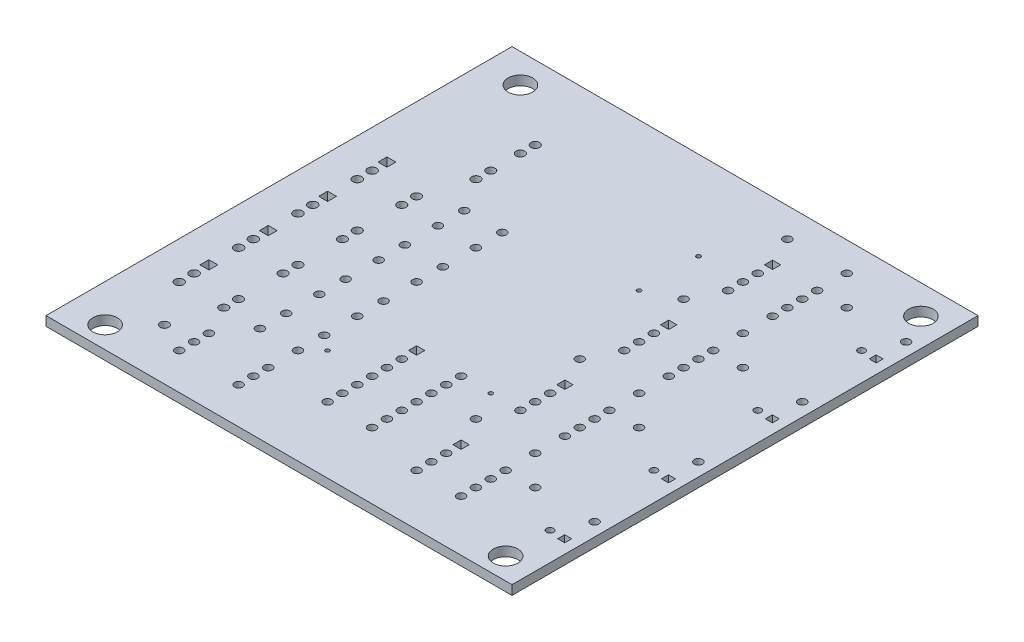
SolidWorks part; units mm, degrees
ref_plane "Front Plane" through (0, 0, 0) normal (0, 0, 1) x (1, 0, 0)
ref_plane "Top Plane" through (0, 0, 0) normal (0, 1, 0) x (1, 0, 0)
ref_plane "Right Plane" through (0, 0, 0) normal (1, 0, 0) x (0, 0, -1)
ref_plane "Plane1" through (0, 1.6, 0) normal (0, 1, 0) x (1, 0, 0)
sketch "Sketch1" plane through (0, 1.6, 0) normal (0, 1, 0) x (1, 0, 0)
  line L0 (54.1498, -45.0785) -> (55.5486, -45.0785)
  line L1 (55.5486, -45.0785) -> (55.5486, -46.4772)
  line L2 (55.5486, -46.4772) -> (54.1498, -46.4772)
  line L3 (54.1498, -46.4772) -> (54.1498, -45.0785)
  line L4 (5.7659, -37.3854) -> (7.2918, -37.3854)
  line L5 (7.2918, -37.3854) -> (7.2918, -38.9113)
  line L6 (7.2918, -38.9113) -> (5.7659, -38.9113)
  line L7 (5.7659, -38.9113) -> (5.7659, -37.3854)
  line L8 (5.7659, -57.7308) -> (7.2918, -57.7308)
  line L9 (7.2918, -57.7308) -> (7.2918, -59.2567)
  line L10 (7.2918, -59.2567) -> (5.7659, -59.2567)
  line L11 (5.7659, -59.2567) -> (5.7659, -57.7308)
  line L12 (5.7659, -27.2127) -> (7.2918, -27.2127)
  line L13 (7.2918, -27.2127) -> (7.2918, -28.7387)
  line L14 (7.2918, -28.7387) -> (5.7659, -28.7387)
  line L15 (5.7659, -28.7387) -> (5.7659, -27.2127)
  line L16 (77.097, -51.4649) -> (77.097, -50.2634)
  line L17 (77.097, -50.2634) -> (78.2985, -50.2634)
  line L18 (78.2985, -50.2634) -> (78.2985, -51.4649)
  line L19 (78.2985, -51.4649) -> (77.097, -51.4649)
  line L20 (36.3476, -52.708) -> (37.7464, -52.708)
  line L21 (37.7464, -52.708) -> (37.7464, -54.1068)
  line L22 (37.7464, -54.1068) -> (36.3476, -54.1068)
  line L23 (36.3476, -54.1068) -> (36.3476, -52.708)
  line L24 (5.7659, -47.5581) -> (7.2918, -47.5581)
  line L25 (7.2918, -47.5581) -> (7.2918, -49.084)
  line L26 (7.2918, -49.084) -> (5.7659, -49.084)
  line L27 (5.7659, -49.084) -> (5.7659, -47.5581)
  line L28 (54.1498, -62.8807) -> (55.5486, -62.8807)
  line L29 (55.5486, -62.8807) -> (55.5486, -64.2795)
  line L30 (55.5486, -64.2795) -> (54.1498, -64.2795)
  line L31 (54.1498, -64.2795) -> (54.1498, -62.8807)
  line L32 (54.1498, -27.2763) -> (55.5486, -27.2763)
  line L33 (55.5486, -27.2763) -> (55.5486, -28.6751)
  line L34 (55.5486, -28.6751) -> (54.1498, -28.6751)
  line L35 (54.1498, -28.6751) -> (54.1498, -27.2763)
  line L36 (54.1498, -9.4741) -> (55.5486, -9.4741)
  line L37 (55.5486, -9.4741) -> (55.5486, -10.8729)
  line L38 (55.5486, -10.8729) -> (54.1498, -10.8729)
  line L39 (54.1498, -10.8729) -> (54.1498, -9.4741)
  line L40 (77.097, -15.8606) -> (77.097, -14.6591)
  line L41 (77.097, -14.6591) -> (78.2985, -14.6591)
  line L42 (78.2985, -14.6591) -> (78.2985, -15.8606)
  line L43 (78.2985, -15.8606) -> (77.097, -15.8606)
  line L44 (77.097, -69.2671) -> (77.097, -68.0656)
  line L45 (77.097, -68.0656) -> (78.2985, -68.0656)
  line L46 (78.2985, -68.0656) -> (78.2985, -69.2671)
  line L47 (78.2985, -69.2671) -> (77.097, -69.2671)
  line L48 (77.097, -33.6627) -> (77.097, -32.4612)
  line L49 (77.097, -32.4612) -> (78.2985, -32.4612)
  line L50 (78.2985, -32.4612) -> (78.2985, -33.6627)
  line L51 (78.2985, -33.6627) -> (77.097, -33.6627)
  line L52 (79.9984, -0.1017) -> (0.1017, -0.1017)
  line L53 (0.1017, -0.1017) -> (0.1017, -79.9984)
  line L54 (0.1017, -79.9984) -> (79.9984, -79.9984)
  line L55 (79.9984, -79.9984) -> (79.9984, -0.1017)
  circle A0 centre (26.8743, -48.9018) radius 0.6994
  circle A1 centre (54.8492, -53.4074) radius 0.6994
  circle A2 centre (26.8743, -53.4075) radius 0.6994
  circle A3 centre (75.1944, -50.8641) radius 0.6008
  circle A4 centre (77.7378, -45.7779) radius 0.6994
  circle A5 centre (62.4787, -40.6915) radius 0.6994
  circle A6 centre (52.306, -40.6915) radius 0.6994
  circle A7 centre (62.4787, -53.4074) radius 0.6994
  circle A8 centre (6.5288, -61.0369) radius 0.763
  circle A9 centre (54.8492, -50.8642) radius 0.6994
  circle A10 centre (6.5288, -50.8642) radius 0.763
  circle A11 centre (62.4787, -48.321) radius 0.6994
  circle A12 centre (54.8492, -48.321) radius 0.6994
  circle A13 centre (62.4787, -45.7779) radius 0.6994
  circle A14 centre (6.5288, -53.4074) radius 0.763
  circle A15 centre (16.7015, -20.3462) radius 0.7375
  circle A16 centre (16.7015, -22.8894) radius 0.7375
  circle A17 centre (29.415, -61.0603) radius 0.3504
  circle A18 centre (47.2265, -15.251) radius 0.3504
  circle A19 centre (47.2265, -25.4395) radius 0.3504
  circle A20 centre (67.5651, -45.7779) radius 0.6994
  circle A21 centre (6.5288, -63.5801) radius 0.763
  circle A22 centre (75.1945, -5.0871) radius 2.1026
  circle A23 centre (75.1945, -76.2959) radius 2.1026
  circle A24 centre (20.366, -53.4075) radius 0.6994
  circle A25 centre (6.5288, -76.2959) radius 2.1026
  circle A26 centre (6.5288, -5.0871) radius 2.1026
  circle A27 centre (14.1583, -63.5801) radius 0.7375
  circle A28 centre (6.5288, -30.5189) radius 0.763
  circle A29 centre (14.1583, -50.8642) radius 0.7375
  circle A30 centre (14.1583, -53.4074) radius 0.7375
  circle A31 centre (14.1583, -40.6915) radius 0.7375
  circle A32 centre (14.1583, -43.2347) radius 0.7375
  circle A33 centre (62.4787, -50.8642) radius 0.6994
  circle A34 centre (14.1583, -61.0369) radius 0.7375
  circle A35 centre (14.1583, -30.5189) radius 0.7375
  circle A36 centre (11.6152, -71.2096) radius 0.7375
  circle A37 centre (14.1583, -33.0621) radius 0.7375
  circle A38 centre (16.7015, -12.7167) radius 0.7375
  circle A39 centre (16.7015, -15.2598) radius 0.7375
  circle A40 centre (26.8742, -71.2096) radius 0.6994
  circle A41 centre (16.7015, -71.2096) radius 0.6994
  circle A42 centre (20.366, -48.9018) radius 0.6994
  circle A43 centre (37.047, -55.9506) radius 0.6994
  circle A44 centre (44.6765, -55.9506) radius 0.6994
  circle A45 centre (37.047, -58.4937) radius 0.6994
  circle A46 centre (44.6765, -58.4937) radius 0.6994
  circle A47 centre (37.047, -61.0369) radius 0.6994
  circle A48 centre (44.6765, -61.0369) radius 0.6994
  circle A49 centre (37.047, -63.5801) radius 0.6994
  circle A50 centre (44.6765, -63.5801) radius 0.6994
  circle A51 centre (37.047, -66.1233) radius 0.6994
  circle A52 centre (44.6765, -66.1233) radius 0.6994
  circle A53 centre (37.047, -68.6664) radius 0.6994
  circle A54 centre (44.6765, -68.6664) radius 0.6994
  circle A55 centre (62.4787, -63.5801) radius 0.6994
  circle A56 centre (54.8492, -66.1233) radius 0.6994
  circle A57 centre (62.4787, -66.1233) radius 0.6994
  circle A58 centre (54.8492, -68.6664) radius 0.6994
  circle A59 centre (62.4787, -68.6664) radius 0.6994
  circle A60 centre (54.8492, -71.2096) radius 0.6994
  circle A61 centre (62.4787, -71.2096) radius 0.6994
  circle A62 centre (52.306, -58.4937) radius 0.6994
  circle A63 centre (62.4787, -58.4937) radius 0.6994
  circle A64 centre (16.7015, -73.7528) radius 0.6994
  circle A65 centre (26.8742, -73.7528) radius 0.6994
  circle A66 centre (62.4787, -27.9757) radius 0.6994
  circle A67 centre (54.8492, -30.5189) radius 0.6994
  circle A68 centre (62.4787, -30.5189) radius 0.6994
  circle A69 centre (54.8492, -33.0621) radius 0.6994
  circle A70 centre (62.4787, -33.0621) radius 0.6994
  circle A71 centre (54.8492, -35.6052) radius 0.6994
  circle A72 centre (62.4787, -35.6052) radius 0.6994
  circle A73 centre (52.306, -22.8894) radius 0.6994
  circle A74 centre (62.4787, -22.8894) radius 0.6994
  circle A75 centre (62.4787, -10.1735) radius 0.6994
  circle A76 centre (54.8492, -12.7167) radius 0.6994
  circle A77 centre (62.4787, -12.7167) radius 0.6994
  circle A78 centre (54.8492, -15.2598) radius 0.6994
  circle A79 centre (62.4787, -15.2598) radius 0.6994
  circle A80 centre (54.8492, -17.803) radius 0.6994
  circle A81 centre (62.4787, -17.803) radius 0.6994
  circle A82 centre (52.306, -5.0871) radius 0.6994
  circle A83 centre (62.4787, -5.0871) radius 0.6994
  circle A84 centre (26.8742, -68.6664) radius 0.6994
  circle A85 centre (16.7015, -68.6664) radius 0.6994
  circle A86 centre (75.1944, -15.2598) radius 0.6008
  circle A87 centre (75.1944, -68.6664) radius 0.6008
  circle A88 centre (75.1944, -33.0619) radius 0.6008
  circle A89 centre (26.8743, -63.5802) radius 0.6994
  circle A90 centre (20.366, -63.5802) radius 0.6994
  circle A91 centre (26.8743, -59.0745) radius 0.6994
  circle A92 centre (20.366, -59.0745) radius 0.6994
  circle A93 centre (26.8743, -43.2348) radius 0.6994
  circle A94 centre (20.366, -43.2348) radius 0.6994
  circle A95 centre (26.8743, -38.7291) radius 0.6994
  circle A96 centre (20.366, -38.7291) radius 0.6994
  circle A97 centre (26.8743, -33.0621) radius 0.6994
  circle A98 centre (20.366, -33.0621) radius 0.6994
  circle A99 centre (6.5288, -33.0621) radius 0.763
  circle A100 centre (6.5288, -40.6915) radius 0.763
  circle A101 centre (6.5288, -43.2347) radius 0.763
  circle A102 centre (49.7693, -53.4071) radius 0.3504
  circle A103 centre (44.6765, -53.4074) radius 0.6994
  circle A104 centre (77.7378, -10.1735) radius 0.6994
  circle A105 centre (67.5651, -10.1735) radius 0.6994
  circle A106 centre (77.7378, -27.9757) radius 0.6994
  circle A107 centre (67.5651, -27.9757) radius 0.6994
  circle A108 centre (77.7378, -63.5801) radius 0.6994
  circle A109 centre (67.5651, -63.5801) radius 0.6994
  circle A110 centre (20.366, -28.5563) radius 0.6994
  circle A111 centre (26.8743, -28.5563) radius 0.6994
extrude "Boss-Extrude1" add sketch "Sketch1" against normal blind 1.6
